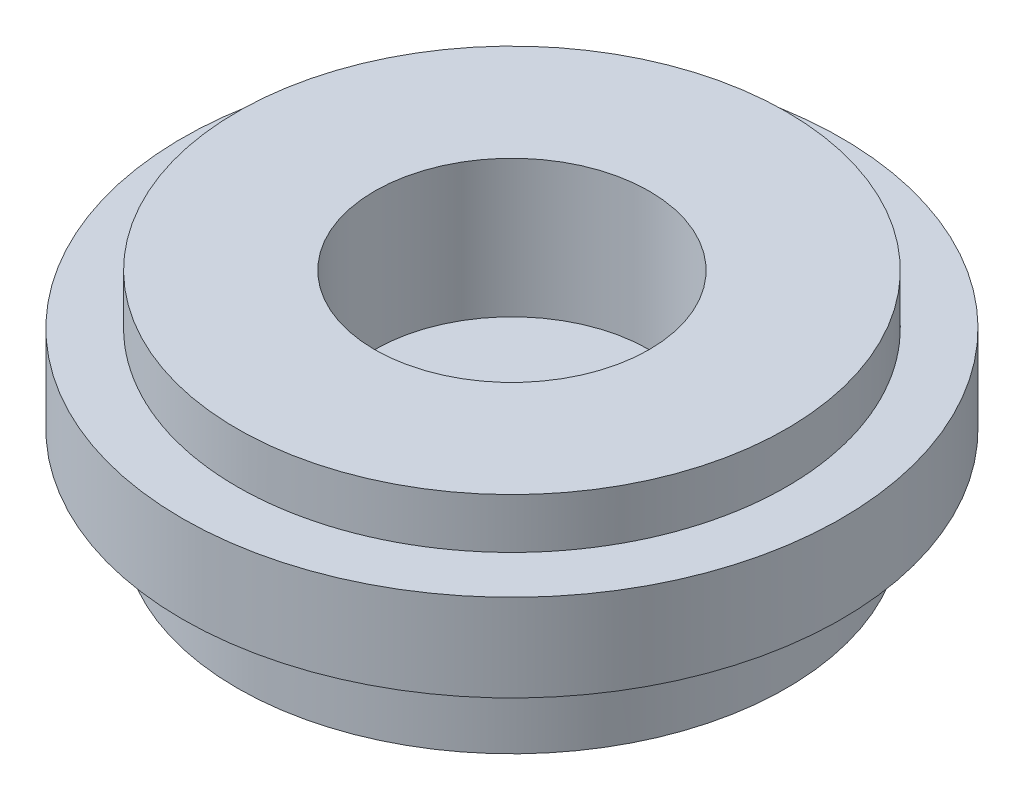
SolidWorks part; units mm, degrees
ref_plane "Front Plane" through (0, 0, 0) normal (0, 0, 1) x (1, 0, 0)
ref_plane "Top Plane" through (0, 0, 0) normal (0, 1, 0) x (1, 0, 0)
ref_plane "Right Plane" through (0, 0, 0) normal (1, 0, 0) x (0, 0, -1)
sketch "Sketch1" plane through (0, 0, 0) normal (0, 1, 0) x (1, 0, 0)
  circle A1 centre (0, 0) radius 5
  dimension "D1" = 10
extrude "Boss-Extrude1" add sketch "Sketch1" along normal blind 1.5875 contours A1
sketch "Sketch4" plane through (0, 1.5875, 0) normal (0, 1, 0) x (1, 0, 0)
  circle A0 centre (0, 0) radius 5
  circle A1 centre (0, 0) radius 5 construction
  circle A2 centre (0, 0) radius 6
  dimension "D1" = 12
extrude "Boss-Extrude4" add sketch "Sketch4" along normal blind 1.5875 separate body
sketch "Sketch2" plane through (0, 1.5875, 0) normal (0, 1, 0) x (1, 0, 0)
  circle A0 centre (0, 0) radius 5
  circle A1 centre (0, 0) radius 2.5
  dimension "D1" = 5
  dimension "D2" = 10
extrude "Boss-Extrude2" add sketch "Sketch2" along normal up to surface (2.5 mm away)
